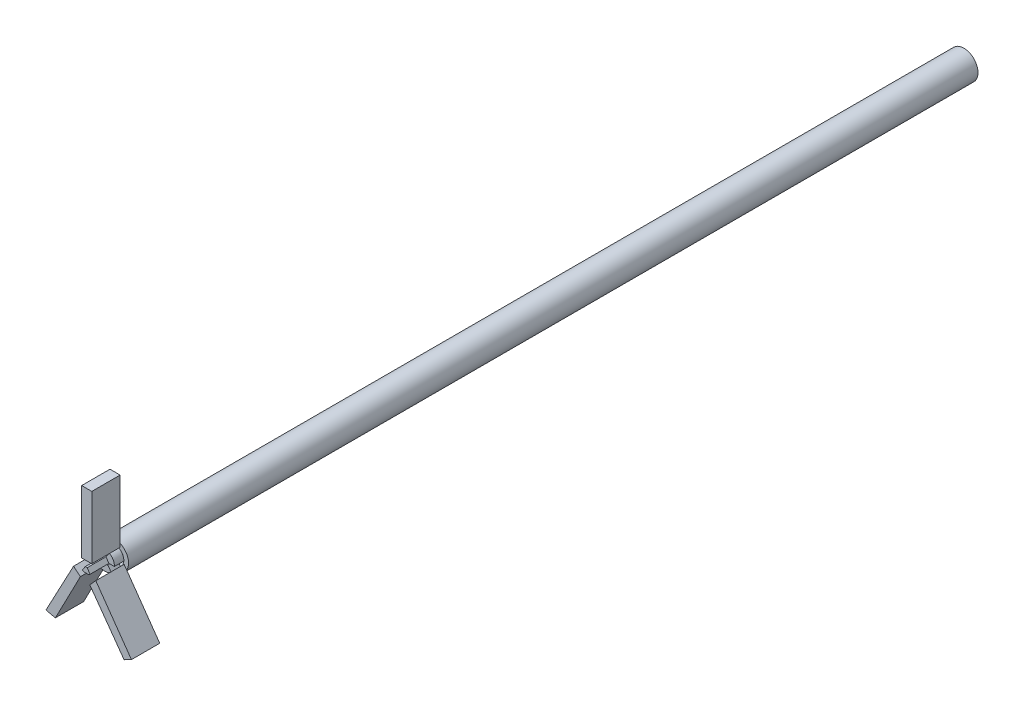
SolidWorks part; units mm, degrees
ref_plane "Front Plane" through (0, 0, 0) normal (0, 0, 1) x (1, 0, 0)
ref_plane "Top Plane" through (0, 0, 0) normal (0, 1, 0) x (1, 0, 0)
ref_plane "Right Plane" through (0, 0, 0) normal (1, 0, 0) x (0, 0, -1)
sketch "Sketch1" plane through (0, 0, 0) normal (0, 0, 1) x (1, 0, 0)
  circle A0 centre (0, 0) radius 10
  circle A1 centre (0, 0) radius 15
  dimension "D1" = 20
  dimension "D2" = 30
extrude "Boss-Extrude1" add sketch "Sketch1" along normal blind 900
sketch "Sketch2" plane through (0, 0, 900) normal (0, 0, 1) x (1, 0, 0)
  line L0 (-0.8548, 3.8761) -> (1.1452, 3.8761)
  line L6 (1.1452, 3.8761) -> (4.1938, -0.6566)
  line L7 (4.1938, -0.6566) -> (2.5342, -1.7728)
  line L8 (2.5342, -1.7728) -> (-2.0475, -1.5972)
  line L9 (-2.0475, -1.5972) -> (-3.8125, -0.6566)
  line L10 (-3.8125, -0.6566) -> (-0.8548, 3.8761)
  line L11 (-4.6637, 9.8802) -> (-4.6637, 76.3475)
  line L12 (-4.6637, 76.3475) -> (6.0692, 76.3475)
  line L13 (-4.6637, 9.8802) -> (6.0692, 9.98)
  line L14 (10.3066, -3.4665) -> (48.0757, -57.0208)
  line L15 (3.9456, -10.4231) -> (40.3038, -61.029)
  line L16 (40.3038, -61.029) -> (48.0757, -57.0208)
  line L17 (-5.999, -7.9437) -> (-32.5604, -59.0836)
  line L18 (-13.2321, -1.9283) -> (-42.4456, -56.7499)
  line L19 (-42.4456, -56.7499) -> (-32.5604, -59.0836)
  line L20 (6.0692, 76.3475) -> (6.0692, 9.98)
  line L21 (10.3066, -3.4665) -> (3.9456, -10.4231)
  line L22 (-13.2321, -1.9283) -> (-5.999, -7.9437)
  dimension "D1" = 2
  dimension "D2" = 2
  dimension "D3" = 2
extrude "Boss-Extrude2" add sketch "Sketch2" along normal blind 30
sketch "Sketch3" plane through (0, 0, 900) normal (0, 0, 1) x (1, 0, 0)
  line L0 (1.1452, 3.8761) -> (4.8046, 8.7702)
  line L1 (4.1938, -0.6566) -> (9.9784, -0.6566)
  line L2 (-2.4955, -2.4598) -> (-5.5414, -8.3242)
  line L3 (3.0469, -2.5155) -> (6.5352, -7.5691)
  line L4 (-0.8548, 3.8761) -> (-4.8046, 8.7702)
  line L5 (-3.8125, -0.6566) -> (-9.9784, -0.6566)
  line L6 (1.1452, 3.8761) -> (-0.8548, 3.8761)
  line L7 (3.0469, -2.5155) -> (2.5342, -2.8694)
  line L8 (2.5342, -2.8694) -> (-2.0475, -2.6925)
  line L9 (-2.0475, -2.6925) -> (-2.4955, -2.4598)
  line L10 (-0.8548, 3.8761) -> (-3.8125, -0.6566)
  line L11 (1.1452, 3.8761) -> (4.1938, -0.6566)
  arc A0 (-4.8046, 8.7702) -> (-9.9784, -0.6566) centre (0, 0) ccw
  arc A1 (9.9784, -0.6566) -> (4.8046, 8.7702) centre (0, 0) ccw
  arc A2 (-5.5414, -8.3242) -> (6.5352, -7.5691) centre (0, 0) ccw
extrude "Boss-Extrude4" add sketch "Sketch3" along normal blind 10 contours L1 A1 L0 L11 | L2 A2 L3 L7 L8 L9 | L10 L5 A0 L4
